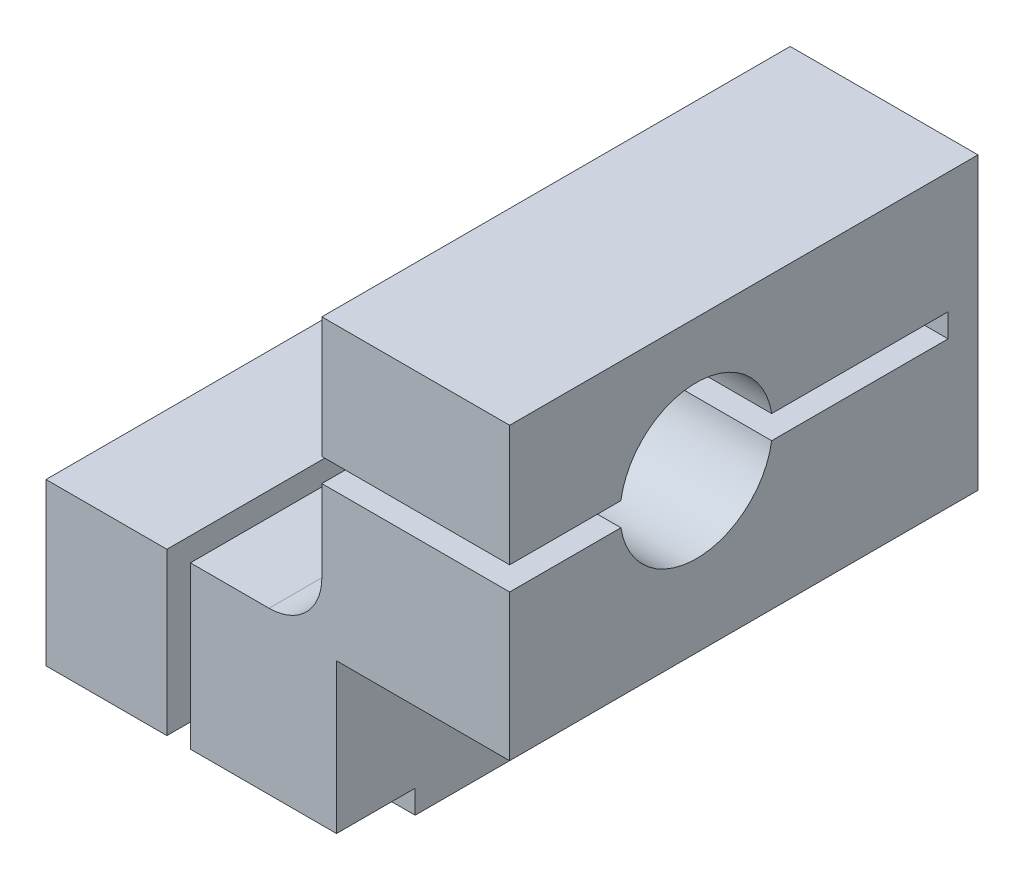
SolidWorks part; units mm, degrees
ref_plane "Front Plane" through (0, 0, 0) normal (0, 0, 1) x (1, 0, 0)
ref_plane "Top Plane" through (0, 0, 0) normal (0, 1, 0) x (1, 0, 0)
ref_plane "Right Plane" through (0, 0, 0) normal (1, 0, 0) x (0, 0, -1)
sketch "Sketch1" plane through (0, 0, 0) normal (0, 0, 1) x (1, 0, 0)
  line L0 (24.75, 0) -> (24.75, 14.75)
  line L1 (0, 0) -> (24.75, 0)
  line L2 (0, 0) -> (0, 15.75)
  line L3 (0, 15.75) -> (19, 15.75)
  line L5 (24.75, 14.75) -> (39.5, 14.75)
  line L6 (23.5, 20.25) -> (23.5, 39.5)
  line L7 (23.5, 39.5) -> (39.5, 39.5)
  line L8 (39.5, 14.75) -> (39.5, 39.5)
  arc A0 (23.5, 20.25) -> (19, 15.75) centre (19, 20.25) cw
  dimension "D1" = 24.75
  dimension "D2" = 24.75
  dimension "D3" = 15.75
  dimension "D4" = 16
  dimension "D5" = 19
  dimension "D6" = 39.5
  dimension "D7" = 39.5
extrude "Boss-Extrude1" add sketch "Sketch1" along normal blind 39.9
sketch "Sketch2" plane through (0, 0, 0) normal (0, -1, 0) x (1, 0, 0)
  line L0 (0, 39.9) -> (24.75, 39.9) construction
  line L1 (10.3, 39.9) -> (12.3, 39.9)
  line L2 (10.3, 39.9) -> (10.3, 22.4226)
  line L3 (10.3, 2.9) -> (12.3, 2.9)
  line L4 (12.3, 39.9) -> (12.3, 22.4226)
  line L5 (0, 39.9) -> (0, 0) construction
  line L6 (24.75, 39.9) -> (24.75, 0) construction
  line L7 (0, 0) -> (24.75, 0) construction
  line L8 (11.3, 2.9) -> (11.3, 16) construction
  line L9 (10.3, 9.5774) -> (10.3, 2.9)
  line L10 (12.3, 9.5774) -> (12.3, 2.9)
  arc A0 (10.3, 22.4226) -> (10.3, 9.5774) centre (11.3, 16) ccw
  arc A1 (12.3, 9.5774) -> (12.3, 22.4226) centre (11.3, 16) ccw
  dimension "D4" = 13
  dimension "D1" = 10.3
  dimension "D2" = 12.45
  dimension "D3" = 37
  dimension "D5" = 16
extrude "Cut-Extrude1" cut sketch "Sketch2" against normal through all both and the other way through all
sketch "Sketch3" plane through (39.5, 0, 0) normal (1, 0, 0) x (0, 0, -1)
  line L0 (-39.9, 14.75) -> (-39.9, 39.5) construction
  line L1 (-39.9, 27.2) -> (-30.4226, 27.2)
  line L2 (-39.9, 27.2) -> (-39.9, 29.2)
  line L3 (-39.9, 29.2) -> (-30.4226, 29.2)
  line L4 (-2.55, 27.2) -> (-2.55, 29.2)
  line L5 (-24, 28.2) -> (-2.55, 28.2) construction
  line L6 (-39.9, 39.5) -> (0, 39.5) construction
  line L7 (-39.9, 14.75) -> (0, 14.75) construction
  line L8 (0, 14.75) -> (0, 39.5) construction
  line L9 (-17.5774, 29.2) -> (-2.55, 29.2)
  line L10 (-17.5774, 27.2) -> (-2.55, 27.2)
  arc A0 (-30.4226, 27.2) -> (-17.5774, 27.2) centre (-24, 28.2) ccw
  arc A1 (-17.5774, 29.2) -> (-30.4226, 29.2) centre (-24, 28.2) ccw
  dimension "D1" = 13
  dimension "D2" = 10.3
  dimension "D3" = 12.45
  dimension "D4" = 37.35
  dimension "D5" = 24
extrude "Cut-Extrude2" cut sketch "Sketch3" against normal through all both
hole_wizard "M4 Tapped Hole1" positions "Sketch4" profile "Sketch5" tap size "M4" standard "DIN"
sketch "Sketch4" plane through (0, 0, 0) normal (0, 0, -1) x (-1, 0, 0)
  line L0 (-39.5, 14.75) -> (-39.5, 39.5) construction
  line L1 (0, 0) -> (-24.75, 0) construction
  line L2 (-39.5, 39.5) -> (-23.5, 39.5) construction
  line L3 (0, 15.75) -> (0, 0) construction
  point P0 (-31.75, 31.75)
  point P2 (-7.75, 7.75)
  dimension "D1" = 7.75
  dimension "D2" = 7.75
  dimension "D3" = 7.75
  dimension "D4" = 7.75
  dimension "D5" = 33.9411
sketch "Sketch5" plane through (31.75, 31.75, 0) normal (1, 0, 0) x (0, 1, 0)
  line L0 (0, 0) -> (0, 11.0914)
  line L1 (0, 11.0914) -> (1.65, 10.1)
  line L2 (1.65, 10.1) -> (1.65, 0.375)
  line L3 (1.65, 0.375) -> (2.025, 0)
  line L5 (2.025, 0) -> (0, 0)
  line L6 (-1.65, 0.375) -> (-2.025, 0) construction
  line L10 (0, 11.0914) -> (-1.65, 10.1) construction
  line L11 (0, -6.35) -> (0, 107.95) construction
  dimension "Tap Drill Dia." = 3.3
  dimension "Tap Drill Depth" = 10.1
  dimension "Near C'Sink Dia." = 4.05
  dimension "Near C'Sink Angle" = 90
  dimension "Drill Angle" = 118
cosmetic thread "Hole Thread1" parameters "D1"=8, "D2"=4
cosmetic thread "Hole Thread2" parameters "D1"=8, "D2"=4
sketch "Sketch6" plane through (0, 0, 0) normal (0, -1, 0) x (1, 0, 0)
  line L0 (24.75, 39.9) -> (24.75, 0) construction
  line L1 (0, 39.9) -> (24.75, 39.9)
  line L2 (0, 39.9) -> (0, 33.2)
  line L3 (0, 33.2) -> (24.75, 33.2)
  line L4 (24.75, 39.9) -> (24.75, 33.2)
  dimension "D1" = 6.7
extrude "Cut-Extrude3" cut sketch "Sketch6" against normal blind 2
